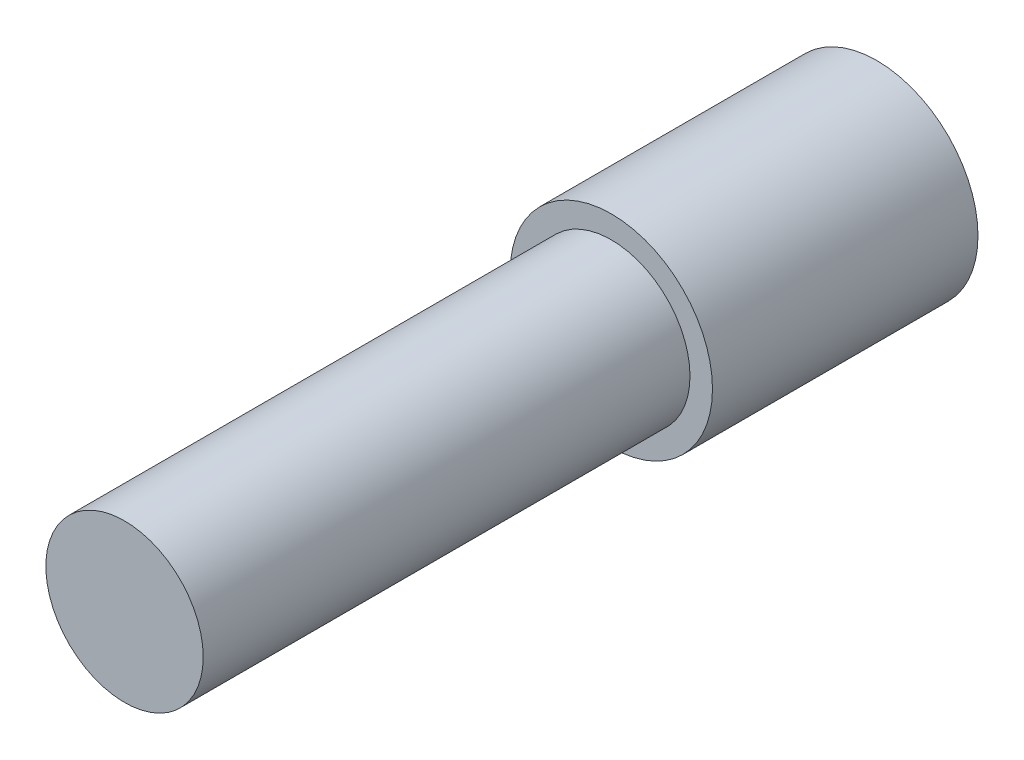
SolidWorks part; units mm, degrees
ref_plane "Front Plane" through (0, 0, 0) normal (0, 0, 1) x (1, 0, 0)
ref_plane "Top Plane" through (0, 0, 0) normal (0, 1, 0) x (1, 0, 0)
ref_plane "Right Plane" through (0, 0, 0) normal (1, 0, 0) x (0, 0, -1)
sketch "Sketch2" plane through (0, 0, 0) normal (0, 0, 1) x (1, 0, 0)
  circle A0 centre (0, 0) radius 2.286
  dimension "D1" = 4.572
extrude "Boss-Extrude1" add sketch "Sketch2" along normal blind 6
sketch "Sketch3" plane through (0, 0, 6) normal (0, 0, 1) x (1, 0, 0)
  circle A1 centre (0, 0) radius 1.778
  dimension "D1" = 3.556
extrude "Boss-Extrude2" add sketch "Sketch3" along normal blind 11
